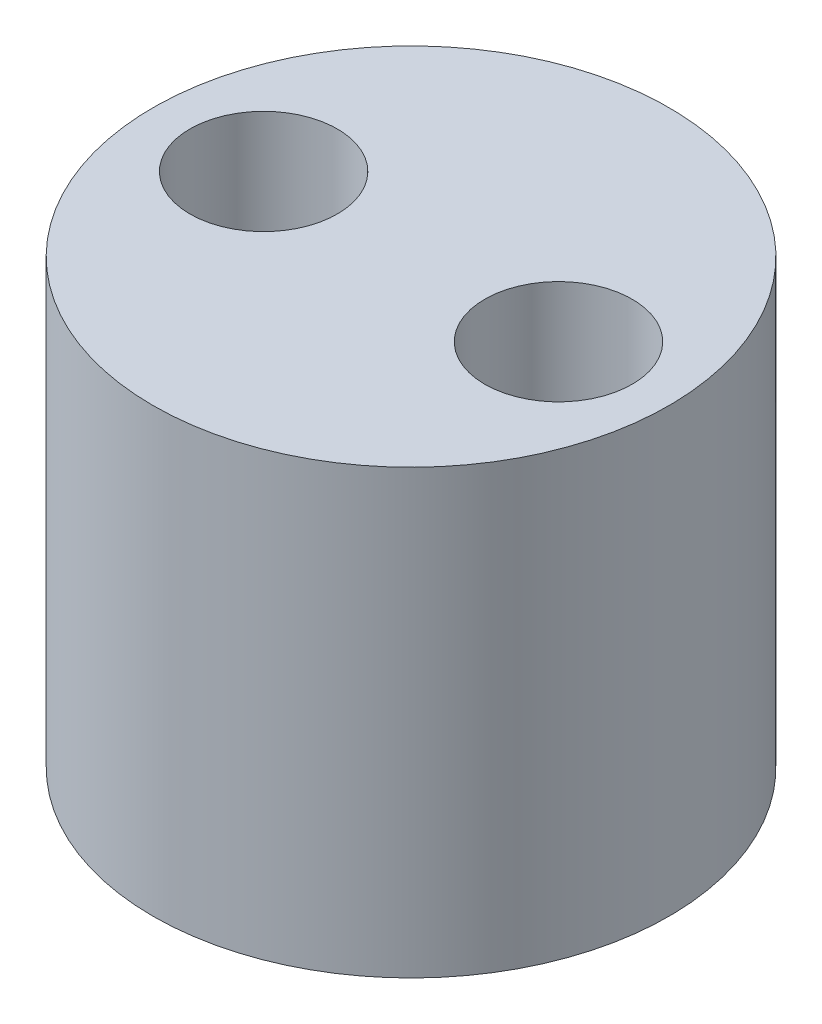
SolidWorks part; units mm, degrees
ref_plane "Front Plane" through (0, 0, 0) normal (0, 0, 1) x (1, 0, 0)
ref_plane "Top Plane" through (0, 0, 0) normal (0, 1, 0) x (1, 0, 0)
ref_plane "Right Plane" through (0, 0, 0) normal (1, 0, 0) x (0, 0, -1)
sketch "Sketch1" plane through (0, 0, 0) normal (0, 1, 0) x (1, 0, 0)
  line L0 (-44.45, 0) -> (44.45, 0) construction
  line L1 (0, 44.45) -> (0, -44.45) construction
  circle A0 centre (0, 0) radius 44.45
  circle A1 centre (-25.4, 0) radius 12.7
  circle A2 centre (25.4, 0) radius 12.7
  dimension "D1" = 88.9
  dimension "D2" = 25.4
  dimension "D3" = 25.4
  dimension "D4" = 25.4
  dimension "D5" = 25.4
extrude "Boss-Extrude2" add sketch "Sketch1" along normal blind 76.2 contours A2 | A1 | A0
